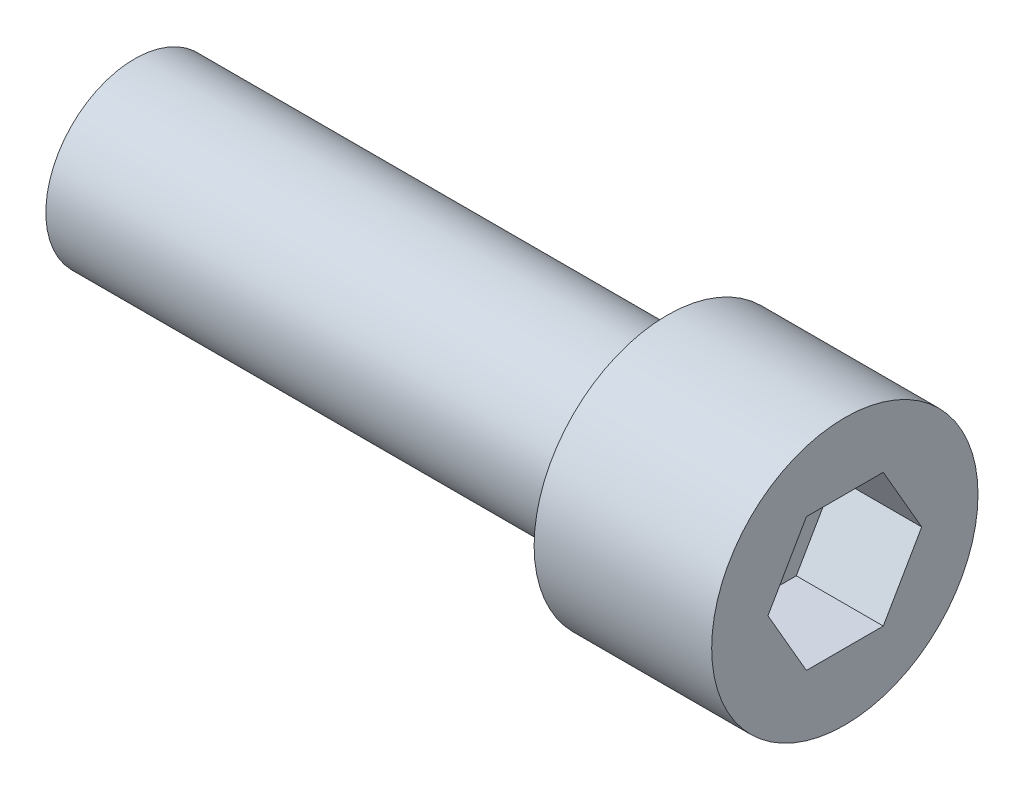
SolidWorks part; units mm, degrees
ref_plane "Front Plane" through (0, 0, 0) normal (0, 0, 1) x (1, 0, 0)
ref_plane "Top Plane" through (0, 0, 0) normal (0, 1, 0) x (1, 0, 0)
ref_plane "Right Plane" through (0, 0, 0) normal (1, 0, 0) x (0, 0, -1)
sketch "Sketch1" plane through (0, 0, 0) normal (1, 0, 0) x (0, 0, -1)
  circle A0 centre (0, 0) radius 6.35
  dimension "D1" = 12.7
extrude "Boss-Extrude1" add sketch "Sketch1" against normal blind 38.1
cosmetic thread "Cosmetic Thread1" parameters "D1"=25.4, "D2"=10.16
sketch "Sketch2" plane through (0, 0, 0) normal (1, 0, 0) x (0, 0, -1)
  circle A0 centre (0, 0) radius 9.525
  dimension "D1" = 19.05
extrude "Boss-Extrude2" add sketch "Sketch2" along normal blind 12.7
sketch "Sketch3" plane through (12.7, 0, 0) normal (1, 0, 0) x (0, 0, -1)
  line L1 (2.7496, 4.7625) -> (-2.7496, 4.7625)
  line L2 (-2.7496, 4.7625) -> (-5.4993, 0)
  line L3 (-5.4993, 0) -> (-2.7496, -4.7625)
  line L4 (-2.7496, -4.7625) -> (2.7496, -4.7625)
  line L5 (2.7496, -4.7625) -> (5.4993, 0)
  line L6 (5.4993, 0) -> (2.7496, 4.7625)
  circle A0 centre (0, 0) radius 4.7625 construction
  point P1 (0, -4.7625)
  dimension "D1" = 9.525
extrude "Cut-Extrude1" cut sketch "Sketch3" against normal blind 6.223
